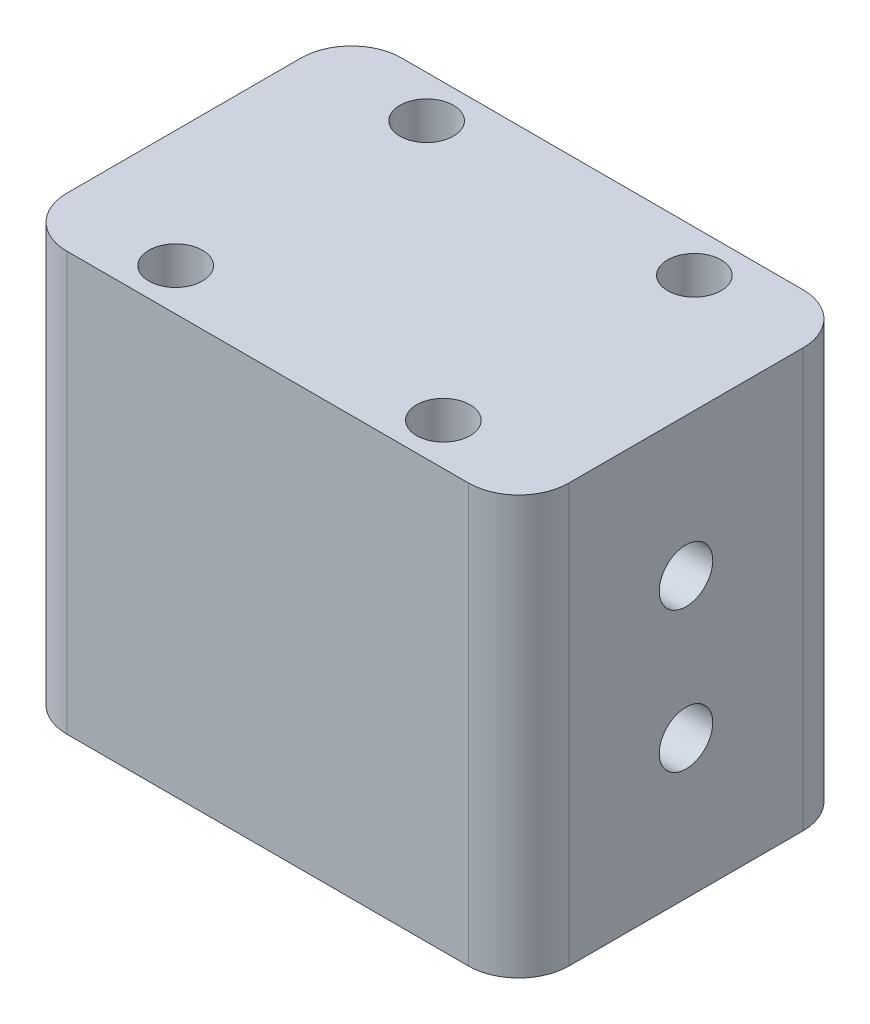
SolidWorks part; units mm, degrees
ref_plane "前视基准面" through (0, 0, 0) normal (0, 0, 1) x (1, 0, 0)
ref_plane "上视基准面" through (0, 0, 0) normal (0, 1, 0) x (1, 0, 0)
ref_plane "右视基准面" through (0, 0, 0) normal (1, 0, 0) x (0, 0, -1)
sketch "草图1" plane through (0, 0, 0) normal (0, 1, 0) x (1, 0, 0)
  line L1 (-15, 10) -> (15, 10)
  line L2 (-15, 10) -> (-15, -10)
  line L3 (-15, -10) -> (15, -10)
  line L4 (15, 10) -> (15, -10)
  line L5 (-15, 10) -> (15, -10) construction
  line L6 (-15, -10) -> (15, 10) construction
  line L7 (-8, 7.5) -> (8, 7.5) construction
  line L8 (-8, 7.5) -> (-8, -7.5) construction
  line L9 (-8, -7.5) -> (8, -7.5) construction
  line L10 (8, 7.5) -> (8, -7.5) construction
  line L11 (-8, 7.5) -> (8, -7.5) construction
  line L12 (-8, -7.5) -> (8, 7.5) construction
  circle A0 centre (-8, 7.5) radius 1.6
  circle A1 centre (-8, -7.5) radius 1.6
  circle A2 centre (8, -7.5) radius 1.6
  circle A3 centre (8, 7.5) radius 1.6
  point P0 (0, 0)
  point P5 (0, 0)
  dimension "D1" = 3.2
  dimension "D2" = 20
  dimension "D3" = 30
  dimension "D4" = 16
  dimension "D5" = 15
extrude "凸台-拉伸1" add sketch "草图1" along normal blind 25
fillet "圆角1" radius 3 4 edges at (15, 12.5, -10) (-15, 12.5, -10) (-15, 12.5, 10) (15, 12.5, 10)
sketch "草图2" plane through (15, 0, 0) normal (1, 0, 0) x (0, 0, -1)
  line L0 (0, 25) -> (0, 0) construction
  line L1 (-7, 25) -> (7, 25) construction
  line L2 (-7, 0) -> (7, 0) construction
  line L3 (0, 25) -> (0, 16.7) construction
  line L4 (0, 0) -> (0, 8.3) construction
  circle A0 centre (0, 16.7) radius 1.6
  circle A1 centre (0, 8.3) radius 1.6
  dimension "D1" = 3.2
  dimension "D2" = 3.2
extrude "切除-拉伸1" cut sketch "草图2" against normal through all
sketch "草图3" plane through (15, 0, 0) normal (1, 0, 0) x (0, 0, -1)
  circle A0 centre (0, 16.7) radius 1.6
  dimension "D1" = 3.2
extrude "凸台-拉伸2" add sketch "草图3" against normal up to surface (30 mm away) up to face at (-15, 16.7, -1.6)
sketch "草图4" plane through (15, 0, 0) normal (1, 0, 0) x (0, 0, -1)
  line L0 (0, 25) -> (0, 16.7) construction
  line L1 (-7, 25) -> (7, 25) construction
  circle A0 centre (0, 16.7) radius 1.6
  dimension "D1" = 3.2
extrude "切除-拉伸2" cut sketch "草图4" against normal through all
